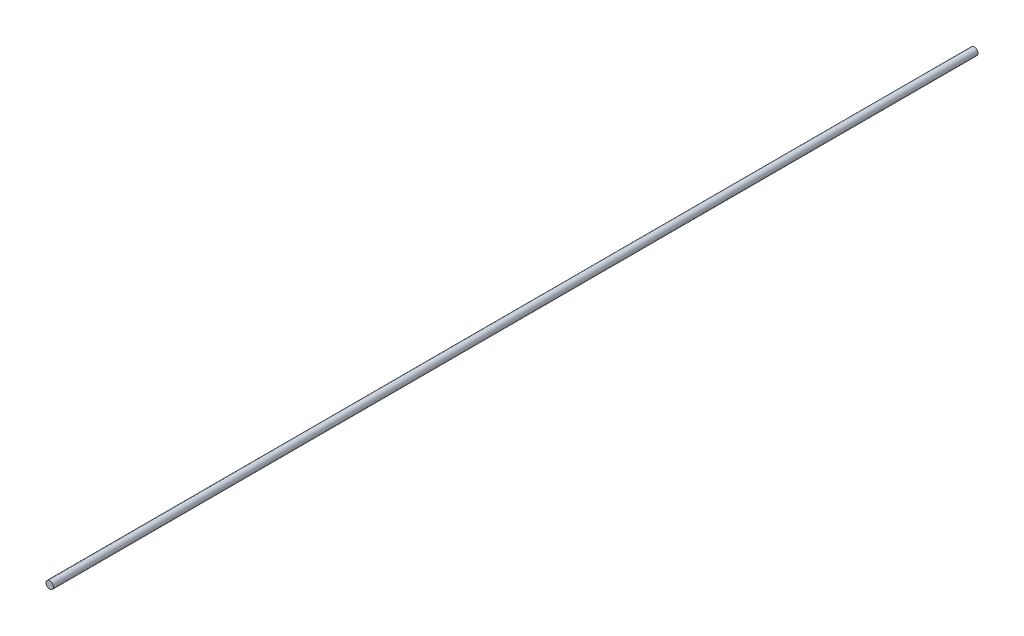
SolidWorks part; units mm, degrees
material "AISI 1020 Steel, Cold Rolled"
ref_plane "Front Plane" through (0, 0, 0) normal (0, 0, 1) x (1, 0, 0)
ref_plane "Top Plane" through (0, 0, 0) normal (0, 1, 0) x (1, 0, 0)
ref_plane "Right Plane" through (0, 0, 0) normal (1, 0, 0) x (0, 0, -1)
sketch "Sketch1" plane through (0, 0, 0) normal (0, 0, 1) x (1, 0, 0)
  circle A0 centre (0, 0) radius 4
  dimension "D1" = 8
extrude "Boss-Extrude1" add sketch "Sketch1" along normal mid plane 1000
cosmetic thread "Cosmetic Thread3"
